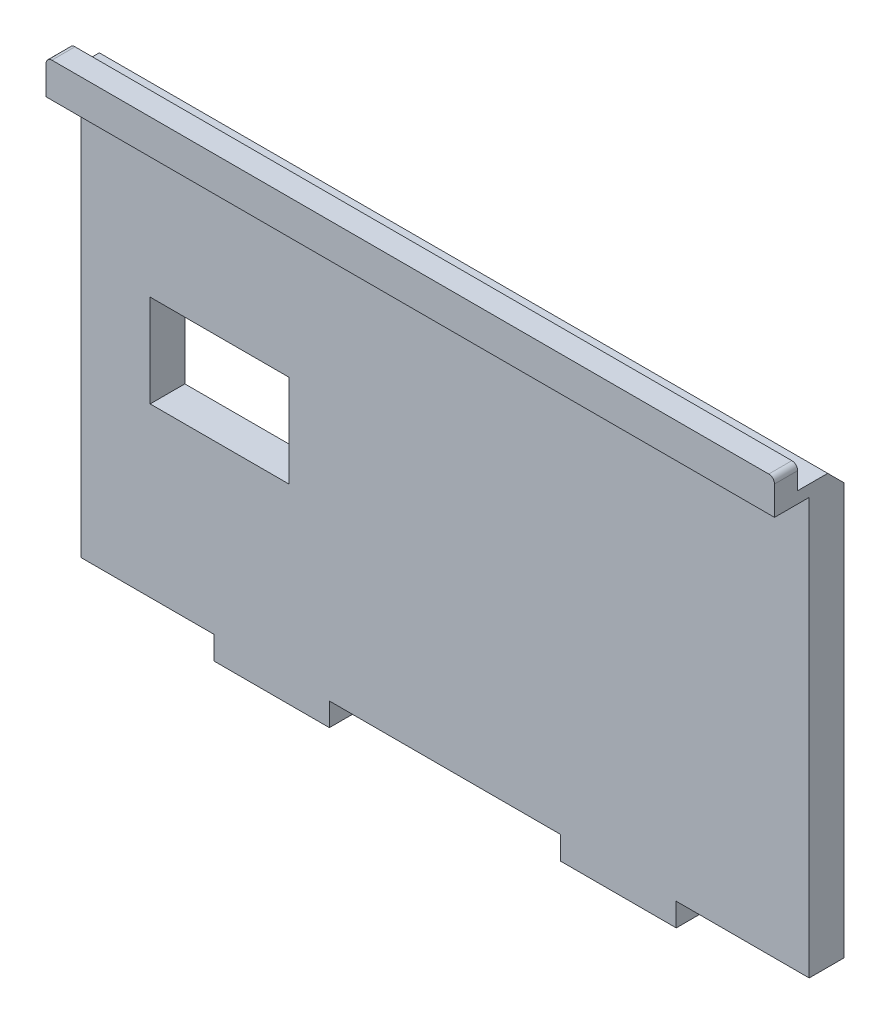
SolidWorks part; units mm, degrees
ref_plane "Front Plane" through (0, 0, 0) normal (0, 0, 1) x (1, 0, 0)
ref_plane "Top Plane" through (0, 0, 0) normal (0, 1, 0) x (1, 0, 0)
ref_plane "Right Plane" through (0, 0, 0) normal (1, 0, 0) x (0, 0, -1)
sketch "Sketch1" plane through (0, 0, 0) normal (0, 0, 1) x (1, 0, 0)
  line L1 (-31.5, -18.5) -> (31.5, -18.5)
  line L2 (-31.5, -18.5) -> (-31.5, 18.5)
  line L3 (-31.5, 18.5) -> (31.5, 18.5)
  line L4 (31.5, -18.5) -> (31.5, 18.5)
  line L5 (-31.5, -18.5) -> (31.5, 18.5) construction
  line L6 (-31.5, 18.5) -> (31.5, -18.5) construction
  point P0 (0, 0)
  dimension "D1" = 63
  dimension "D2" = 37
extrude "Boss-Extrude1" add sketch "Sketch1" along normal blind 3
sketch "Sketch2" plane through (0, -18.5, 0) normal (0, -1, 0) x (1, 0, 0)
  line L0 (0, 3) -> (0, 0) construction
  line L1 (-31.5, 3) -> (31.5, 3) construction
  line L2 (20, 3) -> (10, 1) construction
  line L3 (-20, 1) -> (-10, 1)
  line L4 (-20, 1) -> (-20, 3)
  line L5 (-20, 3) -> (-10, 3)
  line L6 (-10, 1) -> (-10, 3)
  line L7 (-20, 1) -> (-10, 3) construction
  line L8 (-20, 3) -> (-10, 1) construction
  line L9 (20, 1) -> (10, 3) construction
  line L10 (10, 1) -> (10, 3)
  line L11 (20, 3) -> (10, 3)
  line L12 (20, 1) -> (20, 3)
  line L13 (20, 1) -> (10, 1)
  point P5 (-15, 2)
  point P14 (15, 2)
  dimension "D1" = 2
  dimension "D2" = 10
  dimension "D3" = 20
extrude "Boss-Extrude2" add sketch "Sketch2" along normal blind 2
sketch "Sketch3" plane through (0, 0, 3) normal (0, 0, 1) x (1, 0, 0)
  line L0 (-31.5, 18.5) -> (-31.5, -18.5) construction
  line L1 (-31.5, 17.5) -> (31.5, 17.5)
  line L2 (-31.5, 17.5) -> (-31.5, 18.5)
  line L3 (-31.5, 18.5) -> (31.5, 18.5)
  line L4 (31.5, 17.5) -> (31.5, 18.5)
  dimension "D1" = 1
extrude "Boss-Extrude3" add sketch "Sketch3" along normal blind 3
sketch "Sketch4" plane through (0, 0, 3) normal (0, 0, 1) x (1, 0, 0)
  line L0 (-31.5, 6.5) -> (31.5, 6.5) construction
  line L1 (-25.5, -4) -> (-13.5, -4)
  line L2 (-25.5, -4) -> (-25.5, 4)
  line L3 (-25.5, 4) -> (-13.5, 4)
  line L4 (-13.5, -4) -> (-13.5, 4)
  line L5 (-31.5, 17.5) -> (-31.5, -18.5) construction
  dimension "D1" = 2.5
  dimension "D2" = 8
  dimension "D3" = 6
  dimension "D4" = 12
extrude "Cut-Extrude1" cut sketch "Sketch4" against normal through all
sketch "Sketch5" plane through (0, 18.5, 0) normal (0, 1, 0) x (1, 0, 0)
  line L0 (-31.5, -6) -> (-31.5, 0) construction
  line L1 (31.5, -6) -> (-31.5, -6)
  line L2 (31.5, -6) -> (31.5, -4)
  line L3 (31.5, -4) -> (-31.5, -4)
  line L4 (-31.5, -6) -> (-31.5, -4)
  dimension "D1" = 2
extrude "Boss-Extrude4" add sketch "Sketch5" along normal blind 2
chamfer "Chamfer1" distance 1.4 1 edges at (0, 18.5, 0)
fillet "Fillet1" radius 0.5 2 edges at (-31.5, 20.5, 5) (31.5, 20.5, 5)
